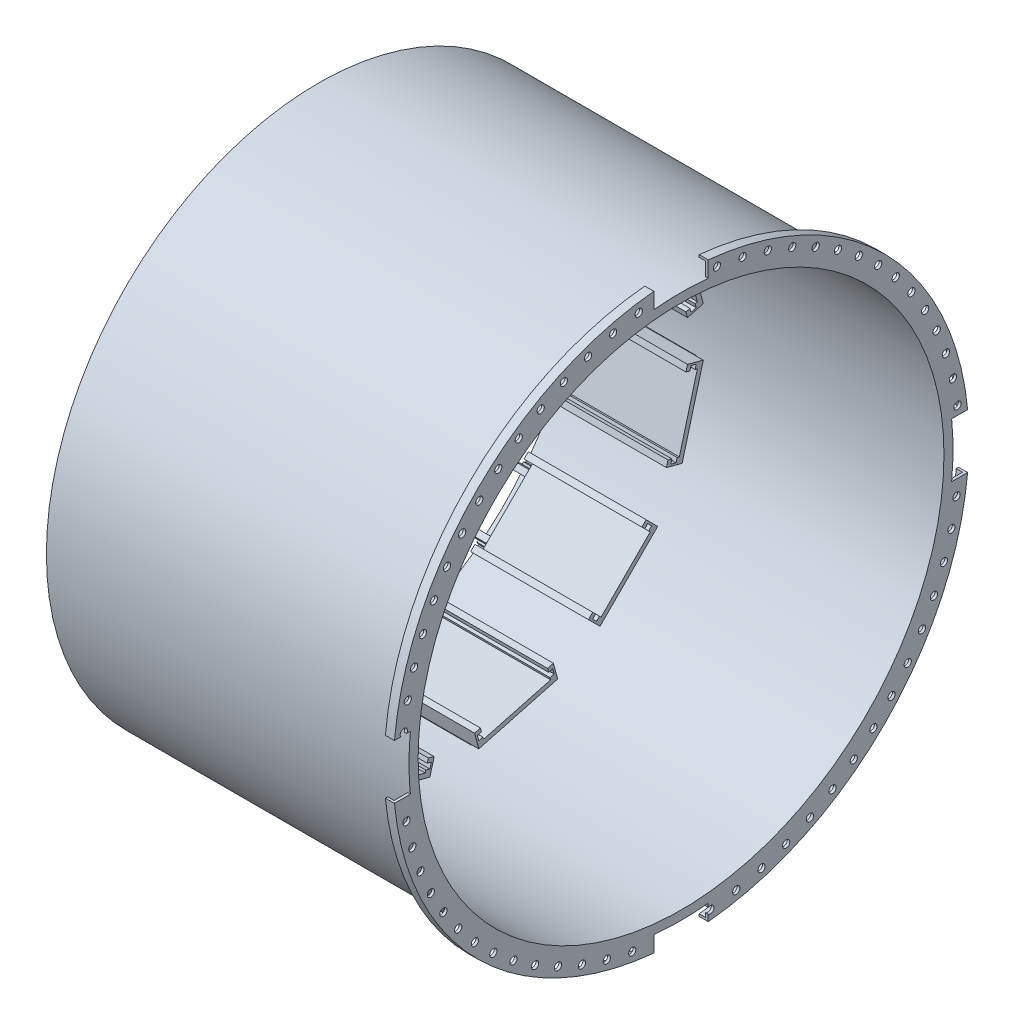
SolidWorks part; units mm, degrees
material "AISI 1035 Steel (SS)"
ref_plane "Front Plane" through (0, 0, 0) normal (0, 0, 1) x (1, 0, 0)
ref_plane "Top Plane" through (0, 0, 0) normal (0, 1, 0) x (1, 0, 0)
ref_plane "Right Plane" through (0, 0, 0) normal (1, 0, 0) x (0, 0, -1)
sketch "Sketch1" plane through (0, 0, 0) normal (0, 0, 1) x (1, 0, 0)
  line L6 (-194.3142, 0) -> (699.045, 0) construction
  line L11 (0, 290) -> (400, 290)
  line L12 (400, 290) -> (400, 317.5)
  line L13 (400, 317.5) -> (390, 317.5)
  line L14 (390, 317.5) -> (390, 315)
  line L15 (390, 315) -> (397, 315)
  line L16 (397, 315) -> (397, 300)
  line L17 (397, 300) -> (0, 300)
  line L18 (0, 300) -> (0, 290)
  line L19 (0, -347.6874) -> (0, 347.6874) construction
  dimension "D8" = 600
  dimension "D9" = 10
  dimension "D10" = 400
  dimension "D11" = 3
  dimension "D12" = 10
  dimension "D13" = 2.5
  dimension "D14" = 27.5
revolve "Revolve1" add sketch "Sketch1" angle 360 about L6
sketch "Sketch2" plane through (0, 0, 0) normal (1, 0, 0) x (0, 0, -1)
  line L0 (316.0795, 30) -> (298.4962, 30)
  line L1 (316.0795, -30) -> (298.4962, -30)
  line L2 (440.5276, 0) -> (300, 0) construction
  line L3 (279.2889, 0) -> (-279.2889, 0) construction
  line L4 (-298.4962, 30) -> (-316.0795, 30)
  line L5 (-300, 0) -> (-428.7577, 0) construction
  line L6 (-298.4962, -30) -> (-316.0795, -30)
  circle A0 centre (0, 0) radius 317.5 construction
  circle A1 centre (0, 0) radius 300 construction
  arc A2 (-316.0795, 30) -> (-316.0795, -30) centre (0, 0) ccw
  arc A3 (-298.4962, 30) -> (-298.4962, -30) centre (0, 0) ccw
  arc A4 (316.0795, -30) -> (316.0795, 30) centre (0, 0) ccw
  arc A5 (298.4962, -30) -> (298.4962, 30) centre (0, 0) ccw
  dimension "D1" = 60
extrude "Cut-Extrude1" cut sketch "Sketch2" along normal through all
pattern_circular "CirPattern1" count 4 over 360 about axis through (0, 0, 0) along (-1, 0, 0) of "Cut-Extrude1"
ref_plane "Plane1" through (20, 0, 0) normal (1, 0, 0) x (0, 0, -1)
sketch "Sketch3" plane through (20, 0, 0) normal (1, 0, 0) x (0, 0, -1)
  line L16 (0, 0) -> (-117.8805, 439.936) construction
  line L17 (0, 220) -> (0, -220) construction
  line L18 (-26.9746, 274.5372) -> (-113.9079, 251.2435)
  line L19 (-113.9079, 251.2435) -> (-109.2492, 233.8569)
  line L20 (-109.2492, 233.8569) -> (-102.8325, 235.5762)
  line L21 (-102.8325, 235.5762) -> (-103.9972, 239.9229)
  line L22 (-103.9972, 239.9229) -> (-108.482, 238.7212)
  line L23 (-108.482, 238.7212) -> (-110.0349, 244.5167)
  line L24 (-110.0349, 244.5167) -> (-105.5501, 245.7184)
  line L25 (-105.5501, 245.7184) -> (-106.1972, 248.1332)
  line L26 (-32.0972, 267.9883) -> (-106.1972, 248.1332)
  line L27 (-31.4501, 265.5735) -> (-32.0972, 267.9883)
  line L28 (-26.9653, 266.7752) -> (-31.4501, 265.5735)
  line L29 (-25.4124, 260.9796) -> (-26.9653, 266.7752)
  line L30 (-29.8972, 259.7779) -> (-25.4124, 260.9796)
  line L31 (-28.7325, 255.4312) -> (-29.8972, 259.7779)
  line L32 (-22.3159, 257.1506) -> (-28.7325, 255.4312)
  line L33 (-26.9746, 274.5372) -> (-22.3159, 257.1506)
  dimension "D1" = 15
  dimension "D3" = 90
  dimension "D4" = 272.1642
  dimension "D6" = 18
  dimension "D12" = 6.643
  dimension "D13" = 4.643
  dimension "D14" = 4.5
  dimension "D15" = 6
  dimension "D16" = 13
extrude "Boss-Extrude1" add sketch "Sketch3" along normal blind 130 separate body
sketch "Sketch4" plane through (0, 0, 0) normal (1, 0, 0) x (0, 0, -1)
  line L38 (0, 0) -> (-491.0381, 0) construction
  line L39 (0, 0) -> (0, 446.2079) construction
  line L40 (-38.357, 282.9873) -> (-43, 282.9873)
  line L41 (-38.357, 286.4873) -> (-38.357, 282.9873)
  line L42 (-38.357, 286.4873) -> (-45, 286.4873)
  line L43 (-45, 271.4873) -> (-45, 286.4873)
  line L44 (-43, 282.9873) -> (-43, 274.9873)
  line L45 (-43, 274.9873) -> (-38.357, 274.9873)
  line L46 (-38.357, 271.4873) -> (-45, 271.4873)
  line L47 (-38.357, 274.9873) -> (-38.357, 271.4873)
  line L48 (-102.5255, 254.2934) -> (-96.7725, 257.6149)
  line L49 (-104.2725, 270.6053) -> (-96.7725, 257.6149)
  line L50 (-110.0255, 267.2838) -> (-104.2725, 270.6053)
  line L51 (-108.2755, 264.2527) -> (-110.0255, 267.2838)
  line L52 (-104.2546, 266.5742) -> (-108.2755, 264.2527)
  line L53 (-100.2546, 259.646) -> (-104.2546, 266.5742)
  line L54 (-104.2755, 257.3245) -> (-100.2546, 259.646)
  line L55 (-102.5255, 254.2934) -> (-104.2755, 257.3245)
  circle A0 centre (0, 0) radius 290 construction
  circle A1 centre (0, 0) radius 290
extrude "Boss-Extrude2" add sketch "Sketch4" along normal blind 130 separate body
pattern_circular "CirPattern9" count 12 over 360 about axis through (0, 0, 0) along (1, 0, 0) of bodies 189 166 127 129 128 165
sketch "Sketch5" plane through (400, 0, 0) normal (1, 0, 0) x (0, 0, -1)
  line L0 (0, 0) -> (302.3942, 302.3942) construction
  line L1 (279.2889, 0) -> (-279.2889, 0) construction
  circle A0 centre (0, 0) radius 307.5 construction
  circle A1 centre (217.4353, 217.4353) radius 4
  dimension "D2" = 615
  dimension "D3" = 8
  dimension "D1" = 45
extrude "Cut-Extrude2" cut sketch "Sketch5" against normal blind 130
pattern_circular "CirPattern10" count 67 over 360 about axis through (0, 0, 0) along (1, 0, 0) of "Cut-Extrude2"
